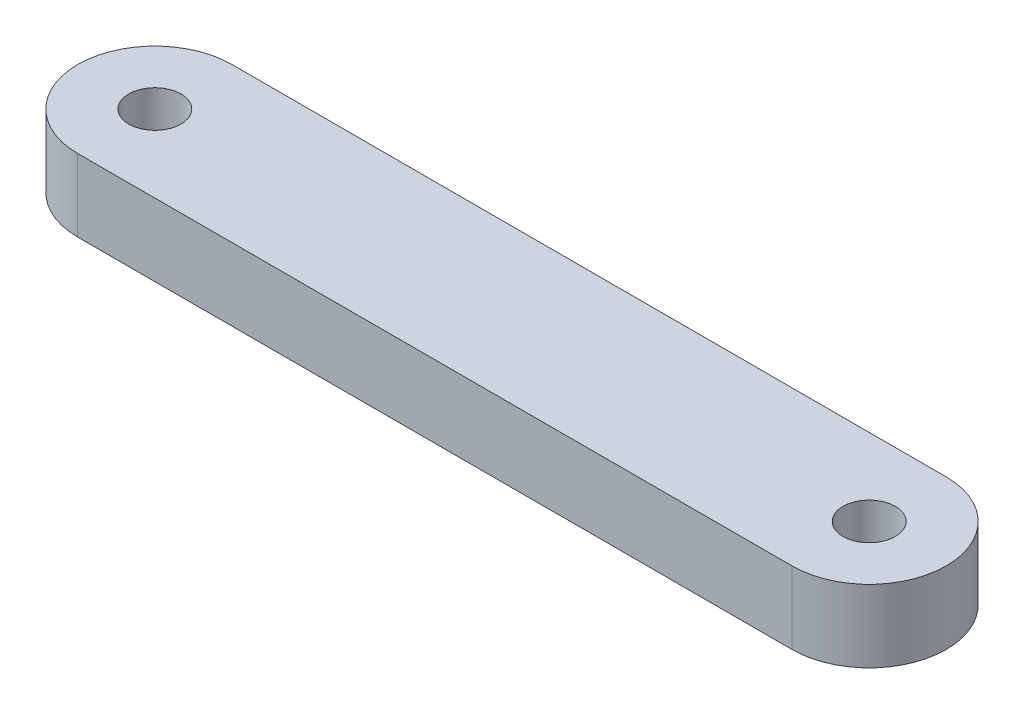
SolidWorks part; units mm, degrees
ref_plane "Front Plane" through (0, 0, 0) normal (0, 0, 1) x (1, 0, 0)
ref_plane "Top Plane" through (0, 0, 0) normal (0, 1, 0) x (1, 0, 0)
ref_plane "Right Plane" through (0, 0, 0) normal (1, 0, 0) x (0, 0, -1)
sketch "Sketch1" plane through (0, 0, 0) normal (0, 1, 0) x (1, 0, 0)
  line L0 (0, 0) -> (-62.6695, 0) construction
  line L1 (0, -6.7652) -> (-62.6695, -6.7652)
  line L2 (0, 6.7652) -> (-62.6695, 6.7652)
  arc A0 (0, -6.7652) -> (0, 6.7652) centre (0, 0) ccw
  arc A1 (-62.6695, 6.7652) -> (-62.6695, -6.7652) centre (-62.6695, 0) ccw
  circle A2 centre (-62.6695, 0) radius 2.2923
  circle A3 centre (0, 0) radius 2.2924
  point P3 (-31.3348, 0)
  point P8 (-69.4348, 0)
  point P9 (6.7652, 0)
  dimension "D2" = 4.5847
  dimension "D3" = 4.5847
  dimension "D1" = 76.2
extrude "Boss-Extrude1" add sketch "Sketch1" along normal blind 6.35
equation "\"kerf\"= 0.01"
